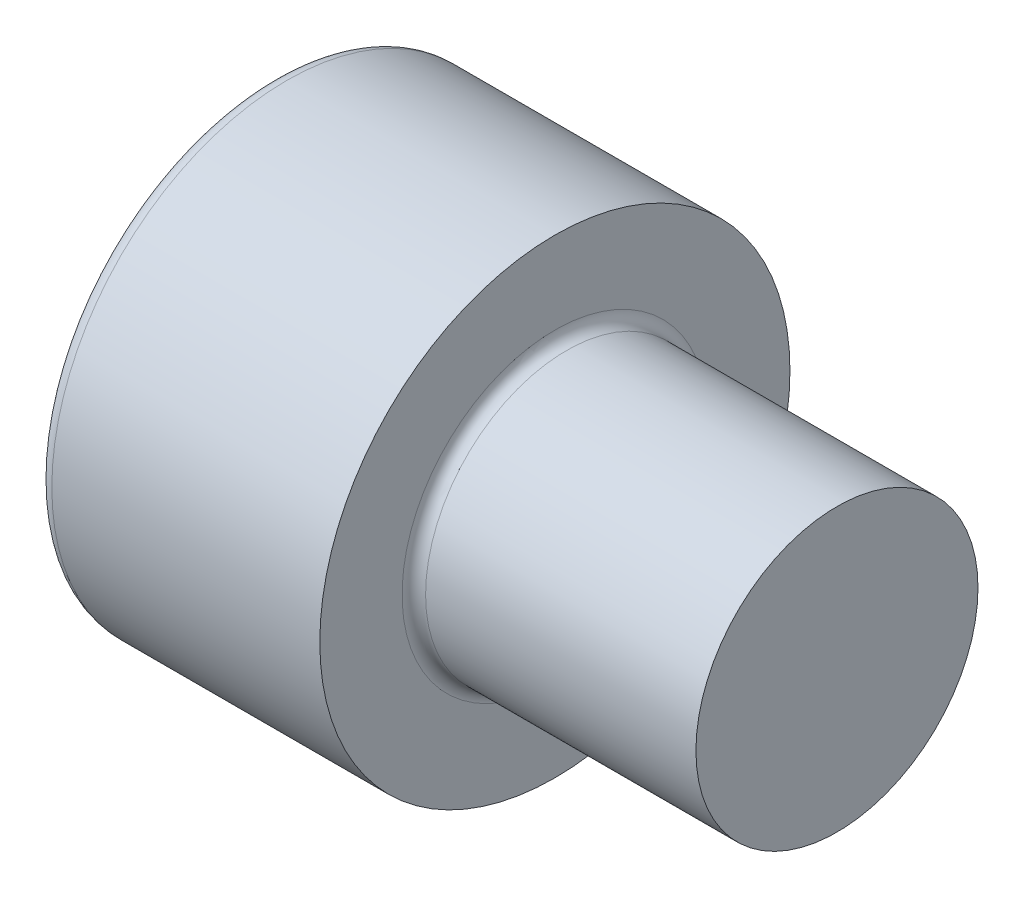
SolidWorks part; units mm, degrees
revolve "Base-Revolve" add sketch "BodySke"
sketch "BodySke" plane through (0, 0, 0) normal (0, 0, 1) x (1, 0, 0)
  line L0 (0, 0) -> (0, 5)
  line L1 (0, 5) -> (6, 5)
  line L2 (6, 5) -> (6, 3)
  line L3 (6, 3) -> (15.4455, 3)
  line L4 (16, 2.4455) -> (16, 0)
  line L5 (16, 0) -> (0, 0)
  line L6 (-31.75, 0) -> (127, 0) construction
  line L8 (16, 2.4455) -> (15.4455, 3)
  line L10 (16, -2.4455) -> (15.4455, -3) construction
  line L11 (7, 9.525) -> (7, 3.175) construction
  line L12 (6, 9.525) -> (6, 3.175) construction
  line L13 (-44, 9.525) -> (-44, 3.175) construction
  dimension "Head_ht" = 6
  dimension "Length" = 10
  dimension "Body_ch_ang" = 45
  dimension "Diameter" = 6
  dimension "Minor_dia" = 4.891
  dimension "Advance" = 1
  dimension "Thread_nom" = 10
  dimension "Thread_length" = 60
  dimension "Head_dia" = 10
cosmetic thread "ThreadCosmetic" [suppressed]
fillet "Fillet1" radius 0.25 1 edges at (6, 0, 3)
fillet "Fillet2" radius 0.3 1 edges at (0, 0, 5)
ref_plane "Plane1" through (0, 0, 0) normal (0, 0, 1) x (1, 0, 0)
ref_plane "Plane2" through (0, 0, 0) normal (0, 1, 0) x (1, 0, 0)
ref_plane "Plane3" through (0, 0, 0) normal (1, 0, 0) x (0, 0, -1)
sketch "Sketch2" plane through (0, 0, 0) normal (0, 0, 1) x (1, 0, 0)
  line L0 (0, 2.542) -> (3, 2.542)
  line L1 (3, 2.542) -> (4.4676, 0)
  line L2 (-31.75, 0) -> (127, 0) construction
  line L3 (4.4676, 0) -> (0, 0)
  line L4 (0, 0) -> (0, 2.542)
  line L6 (0, 0) -> (47.625, 0) construction
  dimension "D1" = 2.542
  dimension "D2" = 60
  dimension "Depth" = 3
revolve "Hex-PreBroach" cut sketch "Sketch2" angle 360 about L6
sketch "Sketch3" plane through (0, 0, 0) normal (-1, 0, 0) x (0, 0.5, 0.866)
  line L0 (1.4676, 2.542) -> (-1.4676, 2.542)
  line L1 (-1.4676, 2.542) -> (-2.9352, 0)
  line L2 (1.4676, 2.542) -> (2.9352, 0)
  line L3 (1.4676, -2.542) -> (2.9352, 0)
  line L4 (1.4676, -2.542) -> (-1.4676, -2.542)
  line L5 (-1.4676, -2.542) -> (-2.9352, 0)
  dimension "D1" = 2.542
  dimension "D2" = 2.542
  dimension "Hex_size" = 5.084
extrude "Hex" cut sketch "Sketch3" against normal blind 3
sketch "ThdSchSke" plane through (0, 0, 0) normal (0, 0, 1) x (1, 0, 0)
  line L0 (9, -2.4455) -> (8.6117, -3)
  line L1 (9, -2.4455) -> (9.3883, -3)
  line L2 (9.3883, -3) -> (9.3883, -3.75)
  line L3 (-3.175, 0) -> (5.1513, 0) construction
  line L4 (0, 4.7) -> (0, -4.7) construction
  line L5 (9.3883, -3.75) -> (8.6117, -3.75)
  line L6 (8.6117, -3.75) -> (8.6117, -3)
  dimension "Thread_minor" = 4.891
  dimension "Diameter" = 6
  dimension "Start" = 9
revolve "ThreadSchematic" [suppressed] cut sketch "ThdSchSke" angle 360 about L3
pattern_linear "ThdSchPat" [suppressed]
sketch "Sketch4" plane through (16, 0, 0) normal (1, 0, 0) x (0, 0, -1)
  circle A0 centre (0, 0) radius 7.8757
extrude "Cut-Extrude1" cut sketch "Sketch4" against normal blind 4
equation "\"D2@Sketch3\" = \"Hex_size@Sketch3\" / 2"
equation "\"D1@Sketch3\" = \"Hex_size@Sketch3\" / 2"
equation "\"D1@Sketch2\" = \"Hex_size@Sketch3\" / 2"
equation "\"Thread_minor@ThreadCosmetic\"  =  \"Minor_dia@BodySke\""
equation "\"Depth@Sketch2\" =  \"Key_eng@Hex\""
equation "\"Thread_length@ThreadCosmetic\" = ((sgn( (\"Length@BodySke\" - \"Advance@BodySke\" * 3.0) - \"Thread_nom@BodySke\" )-1)*( (\"Length@BodySke\" - \"Advance@BodySke\" * 3.0) - \"Thread_nom@BodySke\" ))/-2+ \"Thread_nom@BodySke\""
equation "\"Thread_minor@ThdSchSke\" = \"Minor_dia@BodySke\""
equation "\"Diameter@ThdSchSke\" = \"Diameter@BodySke\""
equation "\"Overcut@ThdSchSke\" = \"Diameter@BodySke\" * 1.25"
equation "\"Start@ThdSchSke\" = \"Head_ht@BodySke\" + \"Length@BodySke\" - \"Thread_length@ThreadCosmetic\"  '---Non-countersunk---"
equation "\"Num_threads@ThdSchPat\" = int( \"Thread_length@ThreadCosmetic\" / \"Advance@BodySke\" + 0.999 )  + 1"
equation "\"Advance@ThdSchPat\" = \"Thread_length@ThreadCosmetic\" /  (\"Num_threads@ThdSchPat\" - 1) 'relax it"
equation "\"Num_threads@ThdSchPat\" = \"Num_threads@ThdSchPat\" - sgn( \"Num_threads@ThdSchPat\" - 1) '---chamfered tips only---"
